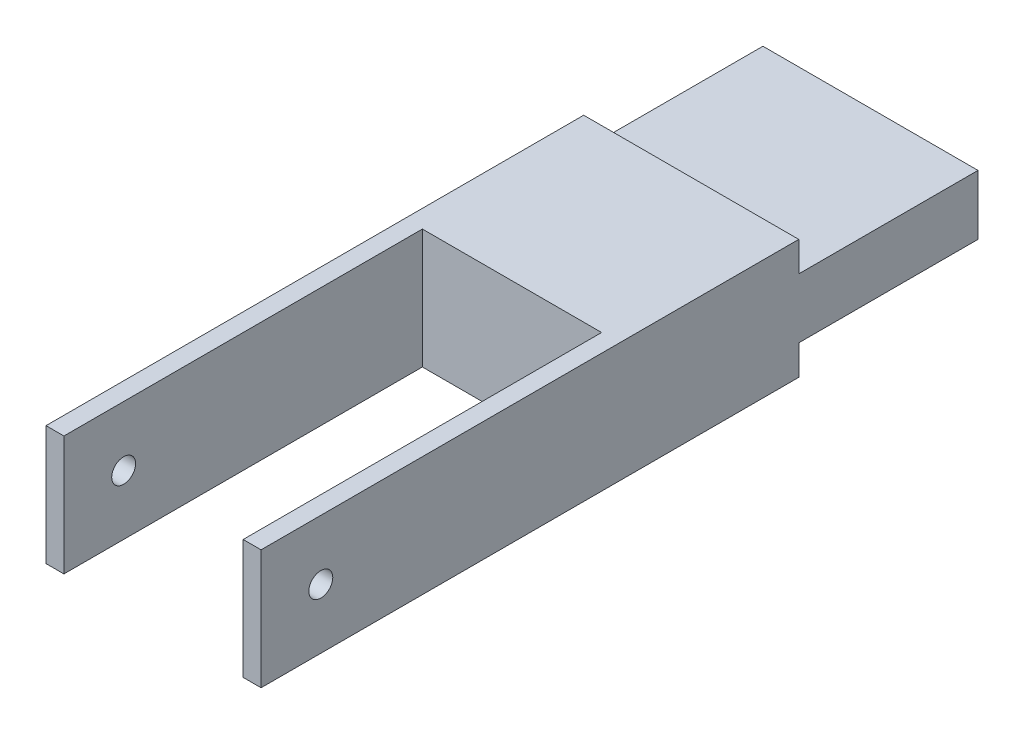
SolidWorks part; units mm, degrees
ref_plane "前视基准面" through (0, 0, 0) normal (0, 0, 1) x (1, 0, 0)
ref_plane "上视基准面" through (0, 0, 0) normal (0, 1, 0) x (1, 0, 0)
ref_plane "右视基准面" through (0, 0, 0) normal (1, 0, 0) x (0, 0, -1)
sketch "草图1" plane through (0, 0, 0) normal (0, 1, 0) x (1, 0, 0)
  line L1 (-18, 60) -> (18, 60)
  line L2 (-18, 60) -> (-18, -60)
  line L3 (-18, -60) -> (18, -60)
  line L4 (18, 60) -> (18, -60)
  line L5 (-18, 60) -> (18, -60) construction
  line L6 (-18, -60) -> (18, 60) construction
  point P0 (0, 0)
  dimension "D1" = 36
  dimension "D2" = 120
extrude "凸台-拉伸1" add sketch "草图1" along normal blind 20
sketch "草图2" plane through (0, 20, 0) normal (0, 1, 0) x (1, 0, 0)
  line L0 (-18, -60) -> (18, -60) construction
  line L1 (15, -76.6423) -> (-15, -76.6423)
  line L2 (15, -76.6423) -> (15, 0)
  line L3 (15, 0) -> (-15, 0)
  line L4 (-15, -76.6423) -> (-15, 0)
  line L5 (18, -60) -> (18, 60) construction
  line L6 (-18, 60) -> (-18, -60) construction
  dimension "D1" = 60
  dimension "D2" = 3
  dimension "D3" = 3
extrude "切除-拉伸1" cut sketch "草图2" against normal blind 20
sketch "草图3" plane through (0, 0, -60) normal (0, 0, -1) x (-1, 0, 0)
  line L0 (-18, 20) -> (18, 20) construction
  line L1 (26.6883, 5) -> (-27.0631, 5)
  line L2 (26.6883, 5) -> (26.6883, -12.7371)
  line L3 (26.6883, -12.7371) -> (-27.0631, -12.7371)
  line L4 (-27.0631, 5) -> (-27.0631, -12.7371)
  line L5 (27.288, 26.3215) -> (-27.1381, 26.3215)
  line L6 (27.288, 26.3215) -> (27.288, 15)
  line L7 (27.288, 15) -> (-27.1381, 15)
  line L8 (-27.1381, 26.3215) -> (-27.1381, 15)
  line L9 (-18, 0) -> (18, 0) construction
  point P10 (0, 20)
  dimension "D1" = 5
  dimension "D2" = 5
extrude "切除-拉伸2" cut sketch "草图3" against normal blind 30
sketch "草图4" plane through (18, 0, 0) normal (1, 0, 0) x (0, 0, -1)
  line L0 (-44.2798, 10) -> (45.4299, 10) construction
sketch "草图5" plane through (18, 0, 0) normal (1, 0, 0) x (0, 0, -1)
  line L0 (-44.2798, 10) -> (45.4299, 10) construction
  line L1 (-60, 20) -> (-60, 0) construction
  circle A0 centre (-50, 10) radius 2
  dimension "D1" = 4
  dimension "D2" = 10
extrude "切除-拉伸3" cut sketch "草图5" against normal blind 70
